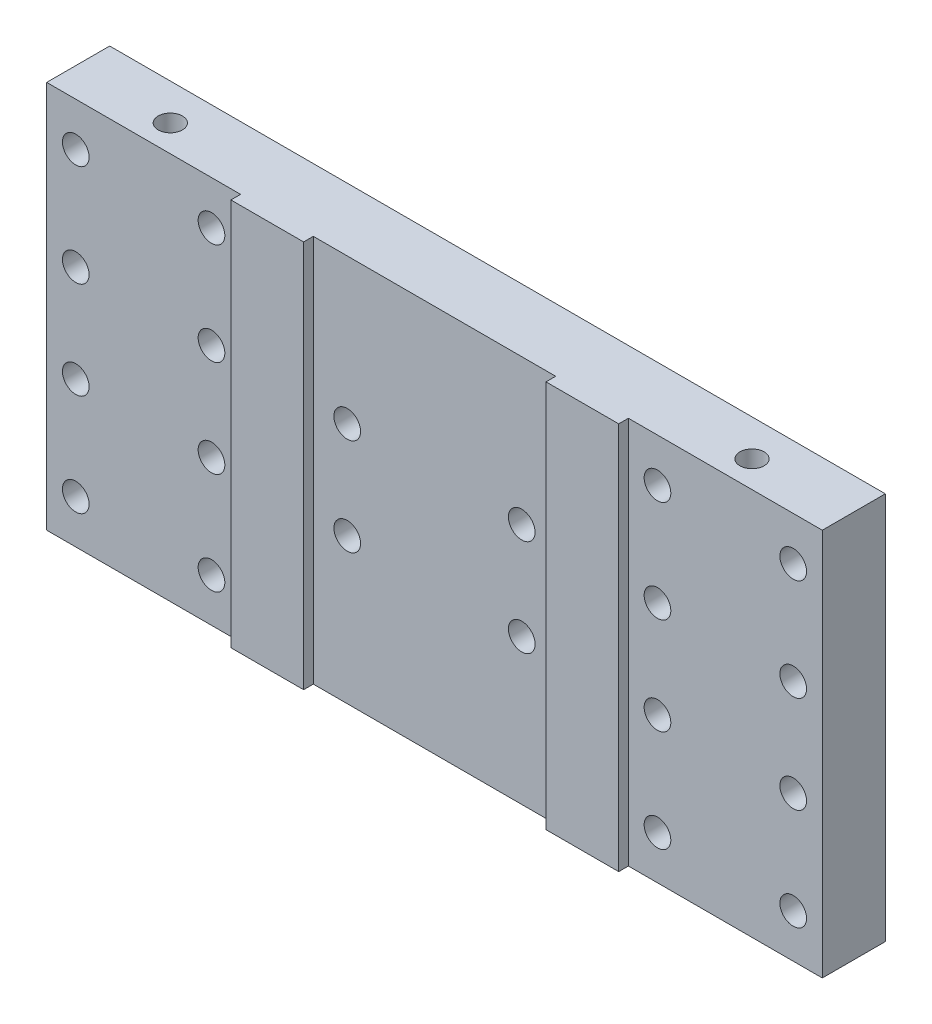
SolidWorks part; units mm, degrees
material "6061 Alloy"
ref_plane "Front Plane" through (0, 0, 0) normal (0, 0, 1) x (1, 0, 0)
ref_plane "Top Plane" through (0, 0, 0) normal (0, 1, 0) x (1, 0, 0)
ref_plane "Right Plane" through (0, 0, 0) normal (1, 0, 0) x (0, 0, -1)
sketch "Sketch1" plane through (0, 0, 0) normal (0, 0, 1) x (1, 0, 0)
  line L0 (0, 42.9856) -> (0, -42.9856) construction
  line L1 (-80, -40) -> (80, -40)
  line L2 (-80, -40) -> (-80, 40)
  line L3 (-80, 40) -> (80, 40)
  line L4 (80, -40) -> (80, 40)
  line L5 (-80, -40) -> (80, 40) construction
  line L6 (-80, 40) -> (80, -40) construction
  line L7 (-80, 0) -> (80, 0) construction
  point P0 (0, 0)
  dimension "D4" = 160
  dimension "D11" = 80
extrude "Boss-Extrude1" add sketch "Sketch1" along normal blind 15
sketch "Sketch10" plane through (0, 0, 0) normal (0, 0, -1) x (-1, 0, 0)
  line L0 (46, 10) -> (74, 10)
  line L1 (-74, 31) -> (-46, 31)
  line L2 (-74, 31) -> (-74, 10)
  line L3 (-74, 10) -> (-46, 10)
  line L4 (-46, 31) -> (-46, 10)
  line L5 (74, 31) -> (74, 10)
  line L6 (46, 31) -> (74, 31)
  line L7 (46, 31) -> (46, 10)
  line L8 (46, -31) -> (74, -31)
  line L9 (74, -10) -> (74, -31)
  line L10 (46, -10) -> (74, -10)
  line L11 (46, -10) -> (46, -31)
  line L12 (-74, -31) -> (-46, -31)
  line L13 (-46, -10) -> (-46, -31)
  line L14 (-74, -10) -> (-46, -10)
  line L15 (-74, -10) -> (-74, -31)
  line L17 (-18, -10) -> (18, -10)
  line L18 (-18, -10) -> (-18, 10)
  line L19 (-18, 10) -> (18, 10)
  line L20 (18, -10) -> (18, 10)
  line L21 (-18, -10) -> (18, 10) construction
  line L22 (-18, 10) -> (18, -10) construction
  circle A0 centre (-74, 31) radius 2.75
  circle A1 centre (-74, 10) radius 2.75
  circle A2 centre (-74, -10) radius 2.75
  circle A3 centre (-74, -31) radius 2.75
  circle A4 centre (74, 31) radius 2.75
  circle A5 centre (74, -10) radius 2.75
  circle A6 centre (74, -31) radius 2.75
  circle A7 centre (74, 10) radius 2.75
  point P4 (0, 0)
  point P22 (46, 20.5)
  dimension "D10" = 5.5
  dimension "D1" = 28
  dimension "D2" = 21
  dimension "D3" = 10
  dimension "D4" = 46
  dimension "D7" = 20
  dimension "D8" = 36
  dimension "D9" = 92
  dimension "D5" = 2
  dimension "D6" = 2
hole_wizard "CBORE for M5 Hex Socket Head Cap Screw1" positions "3DSketch10" profile "Sketch11" counterbore size "M5" standard "ISO"
sketch3d "3DSketch10"
  point P0 (74, 31, 0)
  point P3 (46, 31, 0)
  point P6 (74, 10, 0)
  point P9 (46, 10, 0)
  point P12 (74, -10, 0)
  point P15 (74, -31, 0)
  point P18 (46, -10, 0)
  point P21 (46, -31, 0)
  point P24 (18, -10, 0)
  point P27 (18, 10, 0)
  point P30 (-18, 10, 0)
  point P33 (-18, -10, 0)
  point P36 (-46, 31, 0)
  point P39 (-46, 10, 0)
  point P42 (-74, 31, 0)
  point P45 (-74, 10, 0)
  point P48 (-46, -10, 0)
  point P51 (-46, -31, 0)
  point P54 (-74, -10, 0)
  point P57 (-74, -31, 0)
sketch "Sketch11" plane through (74, 31, 0) normal (1, 0, 0) x (0, 1, 0)
  line L0 (0, 0) -> (0, 16.6514)
  line L1 (0, 16.6514) -> (2.75, 14.999)
  line L2 (2.75, 14.999) -> (2.75, 5.4)
  line L3 (2.75, 5.4) -> (5, 5.4)
  line L4 (5, 5.4) -> (5, 0)
  line L5 (5, 0) -> (0, 0)
  line L10 (0, 16.6514) -> (-2.75, 14.999) construction
  line L11 (0, -6.35) -> (0, 107.95) construction
  dimension "Hole Dia." = 5.5
  dimension "Hole Depth" = 14.999
  dimension "C'Bore Dia." = 10
  dimension "C'Bore Depth" = 5.4
  dimension "Drill Angle" = 118
sketch "Sketch12" plane through (0, -40, 0) normal (0, -1, 0) x (1, 0, 0)
  line L0 (-60, 7.5) -> (60, 7.5)
  line L1 (-80, 15) -> (80, 15) construction
  point P4 (0, 7.5)
  dimension "D1" = 7.5
  dimension "D2" = 120
hole_wizard "M6 Tapped Hole1" positions "3DSketch11" profile "Sketch13" tap size "M6" standard "ISO" end condition through all
sketch3d "3DSketch11"
  point P0 (-60, -40, 7.5)
  point P3 (60, -40, 7.5)
sketch "Sketch13" plane through (-60, -40, 7.5) normal (1, 0, 0) x (0, 0, -1)
  line L0 (0, 0) -> (0, 80)
  line L1 (0, 80) -> (2.5, 80)
  line L2 (2.5, 80) -> (2.5, 0)
  line L5 (2.5, 0) -> (0, 0)
  line L11 (0, -6.35) -> (0, 107.95) construction
  dimension "Thread Major Dia." = 5
  dimension "Thru Tap Drill Depth" = 80
sketch "Sketch14" plane through (0, 0, 0) normal (0, 0, -1) x (-1, 0, 0)
  line L0 (0, 0) -> (0, -40) construction
  line L1 (80, -40) -> (-80, -40) construction
  line L2 (0, 0) -> (-80, 0) construction
  line L3 (-80, -40) -> (-80, 40) construction
  circle A0 centre (-74, 31) radius 2.75
  circle A1 centre (-74, 31) radius 5
  circle A2 centre (-74, 10) radius 2.75
  circle A3 centre (-74, 10) radius 5
  circle A4 centre (74, 10) radius 5
  circle A5 centre (74, 10) radius 2.75
  circle A6 centre (74, 31) radius 5
  circle A7 centre (74, 31) radius 2.75
  circle A8 centre (74, -31) radius 2.75
  circle A9 centre (74, -31) radius 5
  circle A10 centre (74, -10) radius 2.75
  circle A11 centre (74, -10) radius 5
  circle A12 centre (-74, -10) radius 5
  circle A13 centre (-74, -10) radius 2.75
  circle A14 centre (-74, -31) radius 5
  circle A15 centre (-74, -31) radius 2.75
sketch "Sketch15" plane through (0, 0, 15) normal (0, 0, 1) x (1, 0, 0)
  line L0 (-80, -40) -> (80, -40) construction
  line L1 (-80, 40) -> (-40, 40)
  line L2 (-80, 40) -> (-80, -40)
  line L3 (-80, -40) -> (-40, -40)
  line L4 (-40, 40) -> (-40, -40)
  line L5 (-80, 40) -> (-40, -40) construction
  line L6 (-80, -40) -> (-40, 40) construction
  line L7 (0, 0) -> (0, 40) construction
  line L8 (80, 40) -> (-80, 40) construction
  line L9 (80, -40) -> (40, 40) construction
  line L10 (80, 40) -> (40, -40) construction
  line L11 (40, 40) -> (40, -40)
  line L12 (80, -40) -> (40, -40)
  line L13 (80, 40) -> (80, -40)
  line L14 (80, 40) -> (40, 40)
  line L16 (-25, 40) -> (25, 40)
  line L17 (-25, 40) -> (-25, -40)
  line L18 (-25, -40) -> (25, -40)
  line L19 (25, 40) -> (25, -40)
  line L20 (-25, 40) -> (25, -40) construction
  line L21 (-25, -40) -> (25, 40) construction
  point P4 (-60, 0)
  point P17 (60, 0)
  dimension "D1" = 40
  dimension "D2" = 50
extrude "Cut-Extrude1" cut sketch "Sketch15" against normal blind 2
